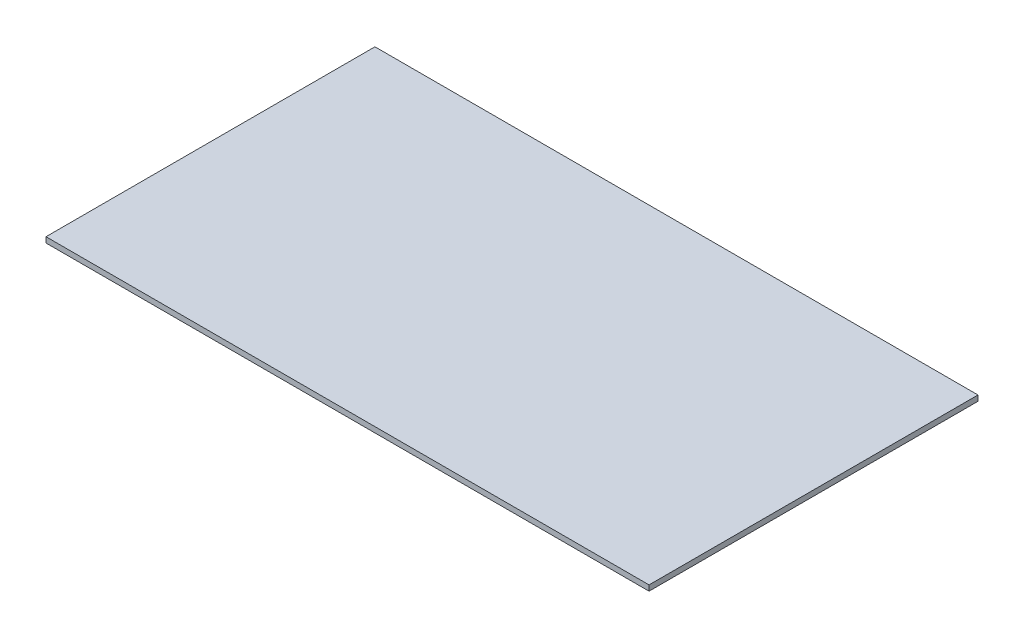
SolidWorks part; units mm, degrees
ref_plane "Front Plane" through (0, 0, 0) normal (0, 0, 1) x (1, 0, 0)
ref_plane "Top Plane" through (0, 0, 0) normal (0, 1, 0) x (1, 0, 0)
ref_plane "Right Plane" through (0, 0, 0) normal (1, 0, 0) x (0, 0, -1)
sketch "Sketch1" plane through (0, 0, 0) normal (0, 1, 0) x (1, 0, 0)
  line L1 (-275, -150) -> (275, -150)
  line L2 (-275, -150) -> (-275, 150)
  line L3 (-275, 150) -> (275, 150)
  line L4 (275, -150) -> (275, 150)
  line L5 (-275, -150) -> (275, 150) construction
  line L6 (-275, 150) -> (275, -150) construction
  point P0 (0, 0)
  dimension "D1" = 550
  dimension "D2" = 300
extrude "Boss-Extrude1" add sketch "Sketch1" along normal blind 5
